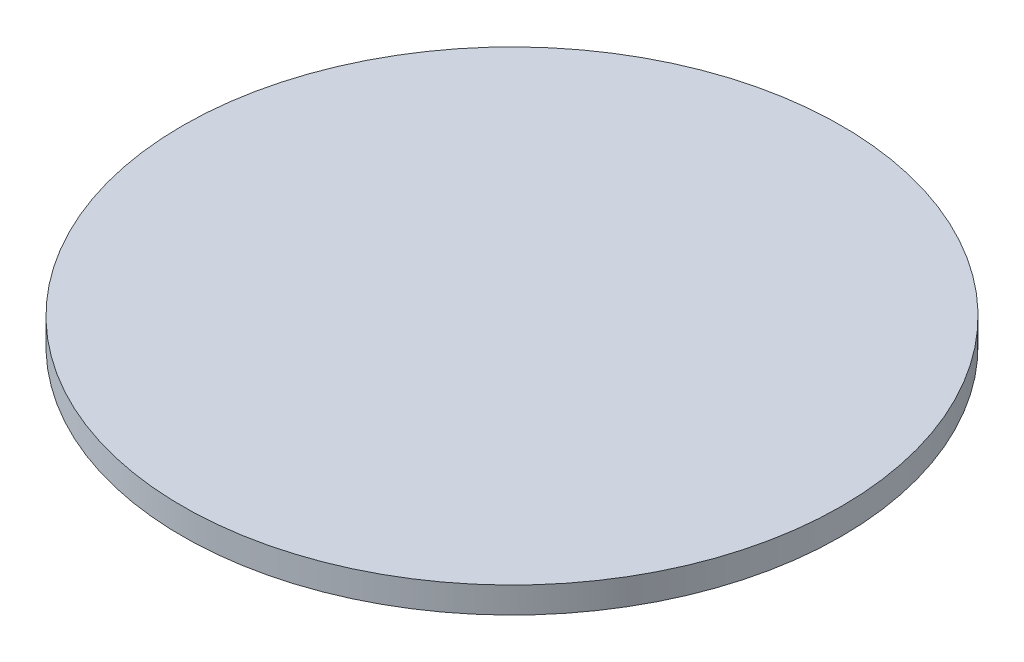
SolidWorks part; units mm, degrees
material "Stainless Steel (ferritic)"
ref_plane "Front Plane" through (0, 0, 0) normal (0, 0, 1) x (1, 0, 0)
ref_plane "Top Plane" through (0, 0, 0) normal (0, 1, 0) x (1, 0, 0)
ref_plane "Right Plane" through (0, 0, 0) normal (1, 0, 0) x (0, 0, -1)
sketch "Sketch1" plane through (0, 0, 0) normal (0, 0, 1) x (1, 0, 0)
  line L0 (0, 0) -> (0, -4)
  line L1 (0, -4) -> (30, -4)
  line L4 (38, -3) -> (38, 0)
  line L5 (38, 0) -> (0, 0)
  arc A0 (30, -4) -> (38, -3) centre (30, 28.5) ccw
  dimension "D1" = 4
  dimension "D2" = 38
  dimension "D3" = 30
  dimension "D4" = 3
revolve "Revolve1" add sketch "Sketch1" angle 360 about L0
